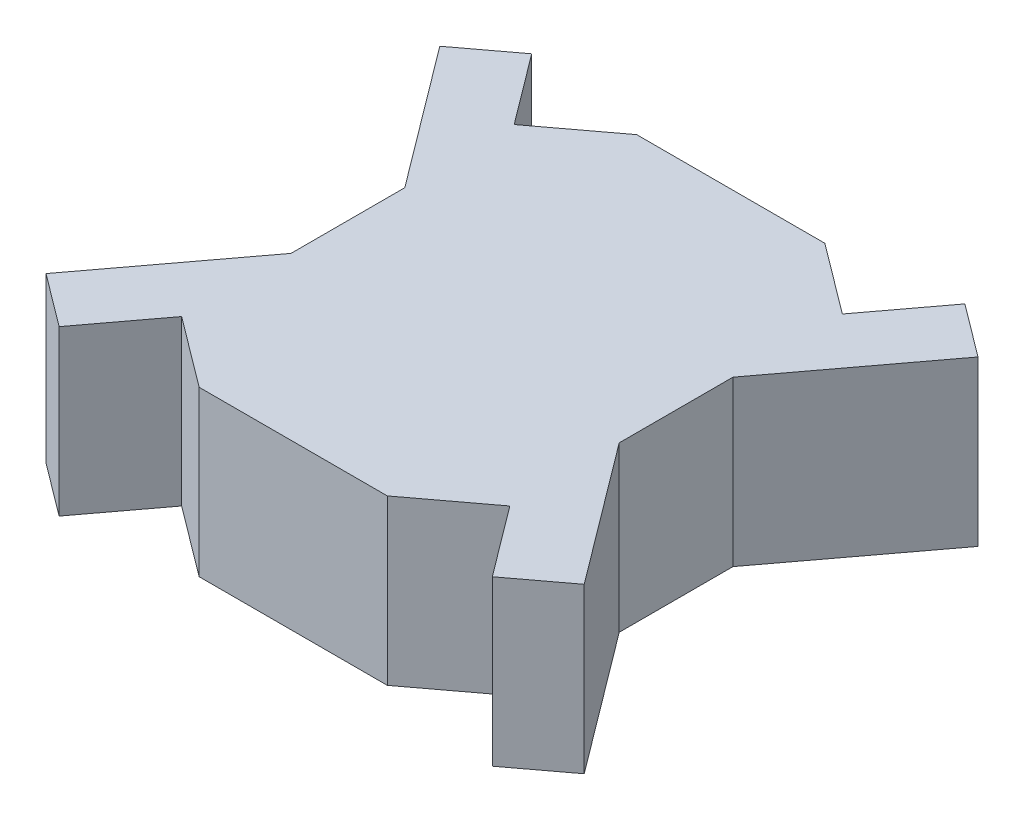
SolidWorks part; units mm, degrees
ref_plane "Front Plane" through (0, 0, 0) normal (0, 0, 1) x (1, 0, 0)
ref_plane "Top Plane" through (0, 0, 0) normal (0, 1, 0) x (1, 0, 0)
ref_plane "Right Plane" through (0, 0, 0) normal (1, 0, 0) x (0, 0, -1)
sketch "Sketch1" plane through (0, 0, 0) normal (0, 1, 0) x (1, 0, 0)
  line L22 (0, 0) -> (0, 52.1485) construction
  line L23 (0, 0) -> (-127.7648, 0) construction
  line L24 (43, 100) -> (-43, 100)
  line L25 (-43, 100) -> (-75, 76)
  line L26 (-75, 76) -> (-99, 108)
  line L27 (-99, 108) -> (-123, 90)
  line L28 (-123, 90) -> (-75, 26)
  line L29 (-75, 26) -> (-75, -26)
  line L30 (-123, -90) -> (-75, -26)
  line L31 (-99, -108) -> (-123, -90)
  line L32 (-75, -76) -> (-99, -108)
  line L33 (-43, -100) -> (-75, -76)
  line L34 (43, -100) -> (-43, -100)
  line L35 (43, -100) -> (75, -76)
  line L36 (75, -76) -> (99, -108)
  line L37 (99, -108) -> (123, -90)
  line L38 (123, -90) -> (75, -26)
  line L39 (75, 26) -> (75, -26)
  line L40 (123, 90) -> (75, 26)
  line L41 (99, 108) -> (123, 90)
  line L42 (75, 76) -> (99, 108)
  line L43 (43, 100) -> (75, 76)
  point P3 (75, 0)
  point P6 (-221.0277, 362.1064)
  point P12 (0, 0)
  point P13 (-422.8772, 370.4098)
  point P14 (-20, 69.4027)
  point P15 (0, 151.6879)
  point P16 (-20, 66.2776)
  point P17 (-20, 22.0581)
  point P18 (-10, 130.4868)
  point P19 (-20, 102.0167)
  point P20 (0, 0)
  point P21 (-10, 65.5571)
  point P22 (-26.469, 23.7033)
  point P23 (-20, 9.8685)
  point P24 (-20, 86.8066)
  point P25 (-105.9798, 100.542)
  point P26 (-120, 101.2675)
  point P28 (-75, 0)
  point P37 (0, -100)
  point P46 (0, 100)
  dimension "D1" = 100
  dimension "D3" = 30
  dimension "D2" = 75
  dimension "D4" = 40
  dimension "D5" = 80
  dimension "D6" = 40
extrude "Boss-Extrude1" add sketch "Sketch1" along normal blind 75 contours L24 L25 L26 L27 L28 L29 L30 L31 L32 L33 L34 L35 L36 L37 L38 L39 L40 L41 L42 L43
equation "\"D5@Sketch1\"=\"D6@Sketch1\"*2"
